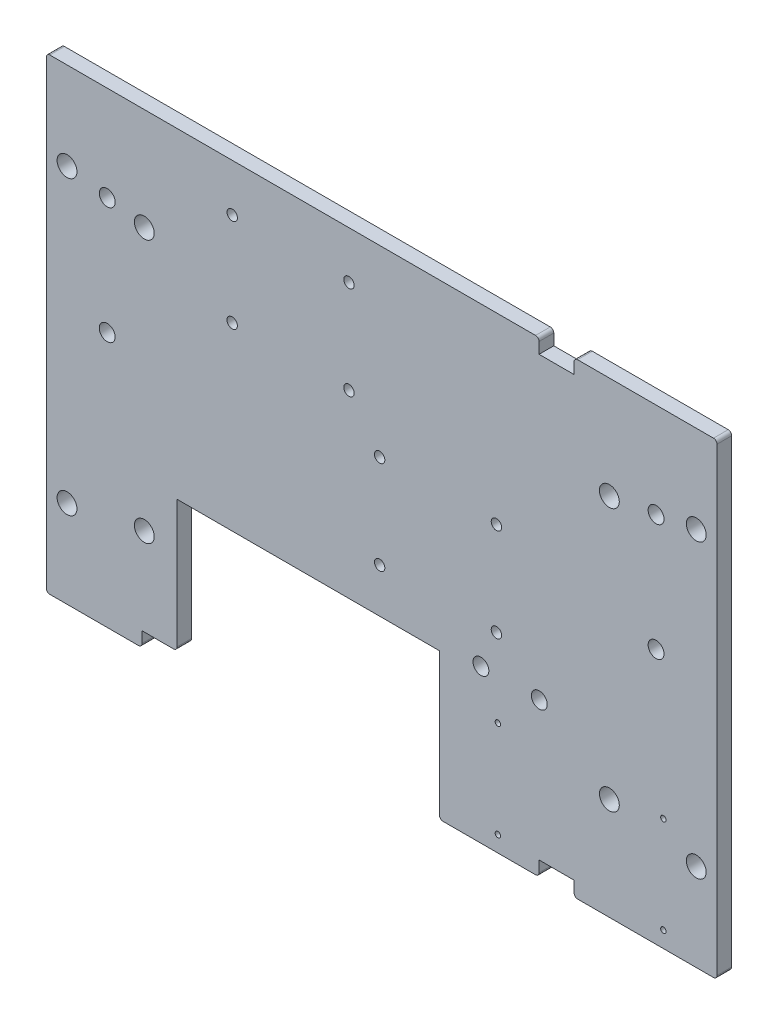
SolidWorks part; units mm, degrees
ref_plane "Front Plane" through (0, 0, 0) normal (0, 0, 1) x (1, 0, 0)
ref_plane "Top Plane" through (0, 0, 0) normal (0, 1, 0) x (1, 0, 0)
ref_plane "Right Plane" through (0, 0, 0) normal (1, 0, 0) x (0, 0, -1)
sketch "Sketch1" plane through (0, 0, 0) normal (0, 0, 1) x (1, 0, 0)
  line L1 (0, 101.6) -> (145.8854, 101.6)
  line L2 (0, 101.6) -> (0, 0)
  line L3 (0, 0) -> (145.8854, 0)
  line L4 (145.8854, 101.6) -> (145.8854, 0)
  dimension "D1" = 101.6
  dimension "D2" = 145.8854
extrude "Boss-Extrude1" add sketch "Sketch1" along normal blind 3.2004
sketch "Sketch4" plane through (0, 0, 3.2004) normal (0, 0, 1) x (1, 0, 0)
  line L0 (0, 101.6) -> (0, 0) construction
  line L1 (28.4328, 31.75) -> (85.5328, 31.75)
  line L2 (28.4328, 31.75) -> (28.4328, 0)
  line L3 (28.4328, 0) -> (85.5328, 0)
  line L4 (85.5328, 31.75) -> (85.5328, 0)
  line L5 (0, 0) -> (145.8854, 0) construction
  dimension "D1" = 28.4328
  dimension "D2" = 57.1
  dimension "D3" = 31.75
extrude "Cut-Extrude1" cut sketch "Sketch4" against normal up to surface (3.2004 mm away) up to face at (72.9427, 50.8, 0)
sketch "Sketch5" plane through (0, 0, 3.2004) normal (0, 0, 1) x (1, 0, 0)
  line L0 (0, 50.8) -> (4.5085, 50.8) construction
  line L1 (4.5085, 19.05) -> (4.5085, 82.55) construction
  line L2 (141.3769, 50.8) -> (145.8854, 50.8) construction
  line L3 (141.3769, 19.05) -> (141.3769, 82.55) construction
  line L4 (0, 101.6) -> (0, 0) construction
  line L5 (145.8854, 0) -> (145.8854, 101.6) construction
  line L6 (21.3199, 50.8) -> (4.5085, 50.8) construction
  line L7 (141.3769, 50.8) -> (122.4729, 50.8) construction
  line L8 (21.3199, 79.375) -> (21.3199, 22.225) construction
  line L9 (122.4729, 79.375) -> (122.4729, 22.225) construction
  line L10 (72.9427, 101.6) -> (72.9427, 0) construction
  line L11 (145.8854, 101.6) -> (0, 101.6) construction
  line L12 (85.5328, 0) -> (145.8854, 0) construction
  circle A0 centre (141.3769, 82.55) radius 2.159
  circle A1 centre (141.3769, 19.05) radius 2.159
  circle A2 centre (4.5085, 19.05) radius 2.159
  circle A3 centre (4.5085, 82.55) radius 2.159
  circle A4 centre (21.3199, 79.375) radius 2.159
  circle A5 centre (21.3199, 22.225) radius 2.159
  circle A6 centre (122.4729, 79.375) radius 2.159
  circle A7 centre (122.4729, 22.225) radius 2.159
  dimension "D3" = 4.318
  dimension "D1" = 4.5085
  dimension "D6" = 4.318
  dimension "D2" = 63.5
  dimension "D4" = 57.15
  dimension "D5" = 21.3199
  dimension "D7" = 23.4124
extrude "Cut-Extrude2" cut sketch "Sketch5" against normal up to surface (3.2004 mm away) up to face at (64.9627, 33.3375, 0)
sketch "Sketch7" plane through (0, 0, 0) normal (0, 0, -1) x (-1, 0, 0)
  line L0 (-40.4382, 91.2945) -> (-40.4382, 70.9745) construction
  line L5 (-65.8382, 91.2945) -> (-65.8382, 70.9745) construction
  line L6 (-40.4382, 81.1345) -> (-65.8382, 81.1345) construction
  line L7 (-72.5075, 61.7201) -> (-72.5075, 41.4001) construction
  line L8 (-97.9075, 61.7201) -> (-97.9075, 41.4001) construction
  line L9 (-72.5075, 51.5601) -> (-97.9075, 51.5601) construction
  circle A0 centre (-40.4382, 91.2945) radius 1.1303
  circle A1 centre (-40.4382, 70.9745) radius 1.1303
  circle A2 centre (-65.8382, 70.9745) radius 1.1303
  circle A3 centre (-65.8382, 91.2945) radius 1.1303
  circle A10 centre (-72.5075, 61.7201) radius 1.1303
  circle A11 centre (-72.5075, 41.4001) radius 1.1303
  circle A12 centre (-97.9075, 41.4001) radius 1.1303
  circle A13 centre (-97.9075, 61.7201) radius 1.1303
  point P13 (-53.1382, 81.1345)
  point P26 (-85.2075, 51.5601)
  dimension "D5" = 2.2606
  dimension "D6" = 2.2606
  dimension "D1" = 25.4
  dimension "D2" = 20.32
  dimension "D3" = 25.4
  dimension "D4" = 20.32
extrude "Cut-Extrude3" cut sketch "Sketch7" against normal up to surface (3.2004 mm away) up to face at (143.5359, 19.05, 3.2004)
sketch "Sketch9" plane through (0, 0, 3.2004) normal (0, 0, 1) x (1, 0, 0)
  line L0 (110.9934, 3.175) -> (110.9934, 98.425) construction
  line L1 (114.8034, 98.425) -> (107.1834, 98.425)
  line L2 (114.8034, 98.425) -> (114.8034, 101.6)
  line L3 (114.8034, 101.6) -> (107.1834, 101.6)
  line L4 (107.1834, 98.425) -> (107.1834, 101.6)
  line L5 (114.8034, 0) -> (107.1834, 0)
  line L6 (114.8034, 0) -> (114.8034, 3.175)
  line L7 (114.8034, 3.175) -> (107.1834, 3.175)
  line L8 (107.1834, 0) -> (107.1834, 3.175)
  line L9 (28.4328, 0) -> (20.8128, 0)
  line L10 (28.4328, 0) -> (28.4328, 3.175)
  line L11 (28.4328, 3.175) -> (20.8128, 3.175)
  line L12 (145.8854, 101.6) -> (0, 101.6) construction
  line L13 (145.8854, 0) -> (145.8854, 101.6) construction
  line L14 (85.5328, 0) -> (145.8854, 0) construction
  line L15 (20.8128, 0) -> (20.8128, 3.175)
  line L16 (0, 0) -> (28.4328, 0) construction
  line L17 (28.4328, 31.75) -> (28.4328, 0) construction
  dimension "D1" = 3.175
  dimension "D2" = 34.892
  dimension "D3" = 7.62
extrude "Cut-Extrude5" cut sketch "Sketch9" against normal up to surface (3.2004 mm away) up to face at (71.3772, 61.7201, 0)
sketch "Sketch10" plane through (0, 0, 3.2004) normal (0, 0, 1) x (1, 0, 0)
  line L0 (116.2328, 0) -> (116.2328, 13.97) construction
  line L1 (134.2328, 13.97) -> (98.2328, 13.97) construction
  line L2 (98.2328, 3.47) -> (98.2328, 24.47) construction
  line L3 (134.2328, 3.47) -> (134.2328, 24.47) construction
  line L4 (114.8034, 0) -> (145.8854, 0) construction
  line L5 (85.5328, 0) -> (85.5328, 31.75) construction
  circle A4 centre (98.2328, 24.47) radius 0.5956
  circle A5 centre (134.2328, 24.47) radius 0.5956
  circle A6 centre (98.2328, 3.47) radius 0.5956
  circle A7 centre (134.2328, 3.47) radius 0.5956
  dimension "D5" = 1.1913
  dimension "D1" = 21
  dimension "D2" = 36
  dimension "D3" = 13.97
  dimension "D4" = 12.7
extrude "Cut-Extrude6" cut sketch "Sketch10" against normal up to surface (3.2004 mm away) up to face at (80.5152, 37.7472, 0)
fillet "Fillet1" radius 0.762 11 edges at (145.8854, 101.6, 1.6002) (114.8034, 101.6, 1.6002) (107.1834, 101.6, 1.6002) (0, 101.6, 1.6002) (0, 0, 1.6002) (85.5328, 0, 1.6002) (107.1834, 0, 1.6002) (114.8034, 0, 1.6002) (145.8854, 0, 1.6002) (20.8128, 0, 1.6002) (28.4328, 3.175, 1.6002)
sketch "Sketch11" plane through (0, 0, 3.2004) normal (0, 0, 1) x (1, 0, 0)
  line L0 (132.6327, 68.2625) -> (13.2527, 68.2625) construction
  line L1 (72.9427, 68.2625) -> (72.9427, 101.6) construction
  line L2 (132.6327, 55.5625) -> (132.6327, 80.9625) construction
  line L3 (13.2527, 55.5625) -> (13.2527, 80.9625) construction
  line L4 (0, 101.6) -> (145.8854, 101.6) construction
  line L5 (107.2327, 33.3375) -> (94.5327, 33.3375) construction
  line L6 (100.8827, 33.3375) -> (100.8827, 68.2625) construction
  circle A0 centre (13.2527, 55.5625) radius 1.7272
  circle A1 centre (13.2527, 80.9625) radius 1.7272
  circle A2 centre (132.6327, 55.5625) radius 1.7272
  circle A3 centre (132.6327, 80.9625) radius 1.7272
  circle A4 centre (107.2327, 33.3375) radius 1.7272
  circle A5 centre (94.5327, 33.3375) radius 1.7272
  dimension "D2" = 3.4544
  dimension "D1" = 25.4
  dimension "D3" = 119.38
  dimension "D4" = 33.3375
  dimension "D5" = 12.7
  dimension "D6" = 34.925
  dimension "D7" = 27.94
extrude "Cut-Extrude7" cut sketch "Sketch11" against normal up to surface (3.2004 mm away) up to face at (98.8284, 24.47, 0)
